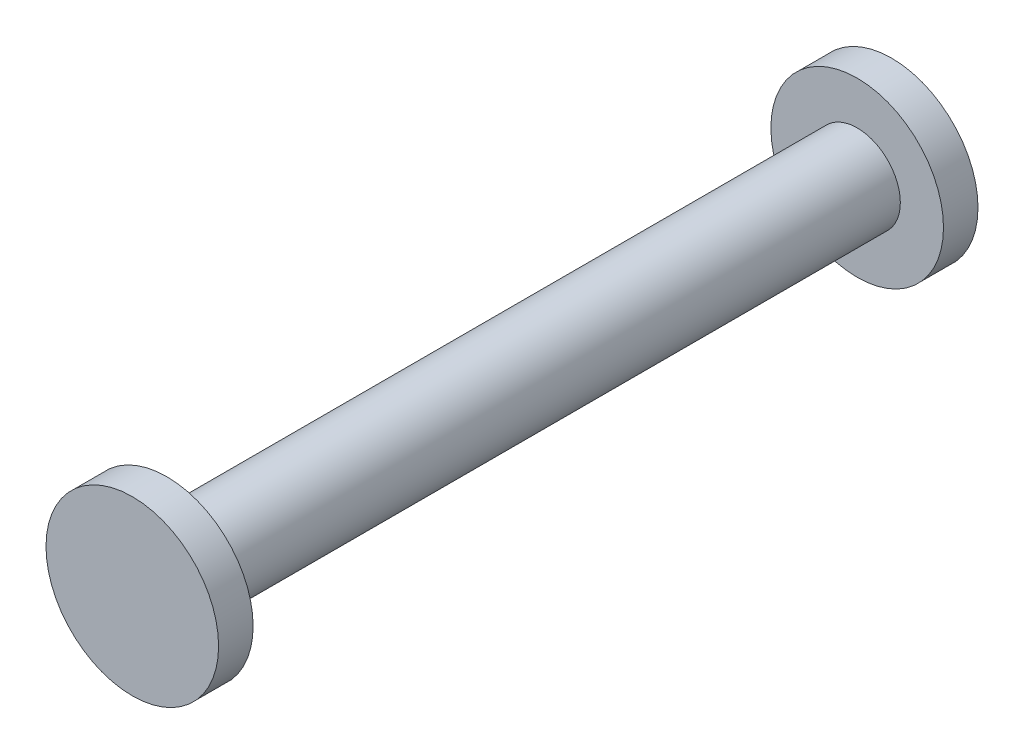
SolidWorks part; units mm, degrees
ref_plane "Front" through (0, 0, 0) normal (0, 0, 1) x (1, 0, 0)
ref_plane "Top" through (0, 0, 0) normal (0, 1, 0) x (1, 0, 0)
ref_plane "Right" through (0, 0, 0) normal (1, 0, 0) x (0, 0, -1)
sketch "Sketch1" plane through (0, 0, 0) normal (0, 0, 1) x (1, 0, 0)
  circle A0 centre (0, 0) radius 3.175
  dimension "D1" = 6.35
extrude "Boss-Extrude1" add sketch "Sketch1" along normal blind 50.8
ref_plane "Plane1" through (0, 0, 25.4) normal (0, 0, 1) x (1, 0, 0)
sketch "Sketch3" plane through (0, 0, 50.8) normal (0, 0, 1) x (1, 0, 0)
  circle A0 centre (0, 0) radius 6.35
  dimension "D1" = 12.7
extrude "Boss-Extrude2" add sketch "Sketch3" along normal blind 2.54
mirror "Mirror1" about plane through (0, 0, 25.4) normal (0, 0, 1) of "Boss-Extrude2"
